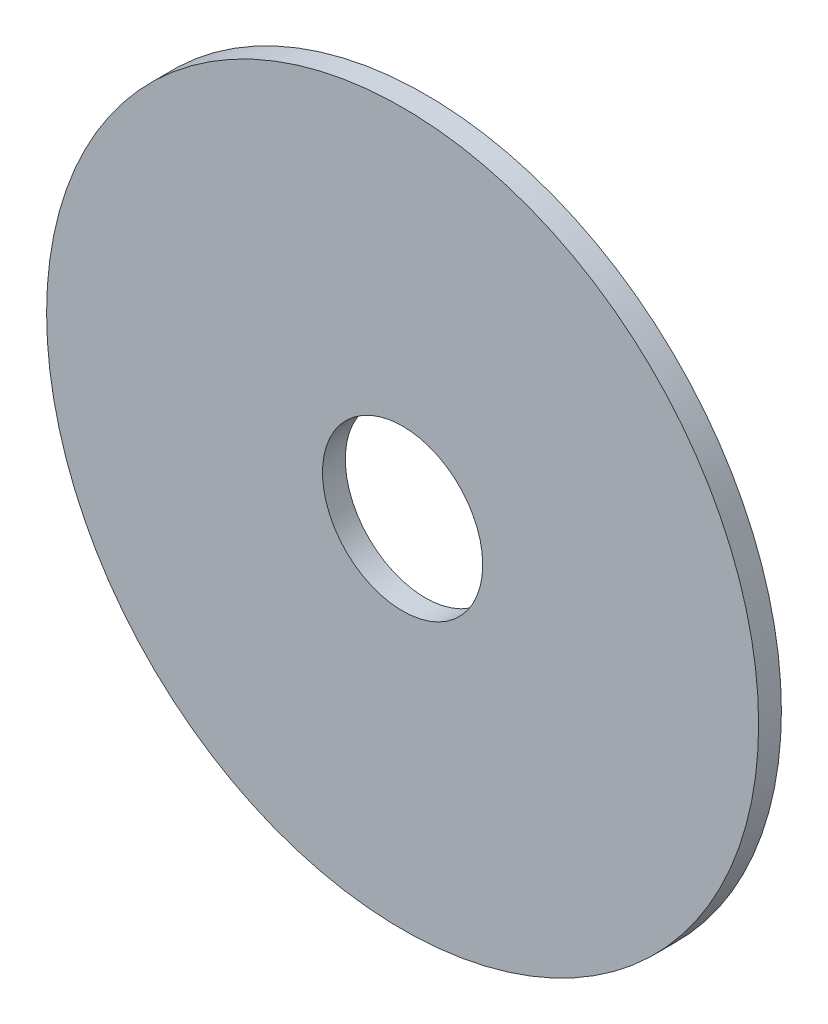
SolidWorks part; units mm, degrees
ref_plane "Front Plane" through (0, 0, 0) normal (0, 0, 1) x (1, 0, 0)
ref_plane "Top Plane" through (0, 0, 0) normal (0, 1, 0) x (1, 0, 0)
ref_plane "Right Plane" through (0, 0, 0) normal (1, 0, 0) x (0, 0, -1)
sketch "Sketch1" plane through (0, 0, 0) normal (0, 0, 1) x (1, 0, 0)
  circle A0 centre (0, 0) radius 3.5719
  circle A1 centre (0, 0) radius 15.875
  dimension "ID" = 7.1437
  dimension "OD" = 31.75
extrude "Extrude1" add sketch "Sketch1" against normal blind 1.016
